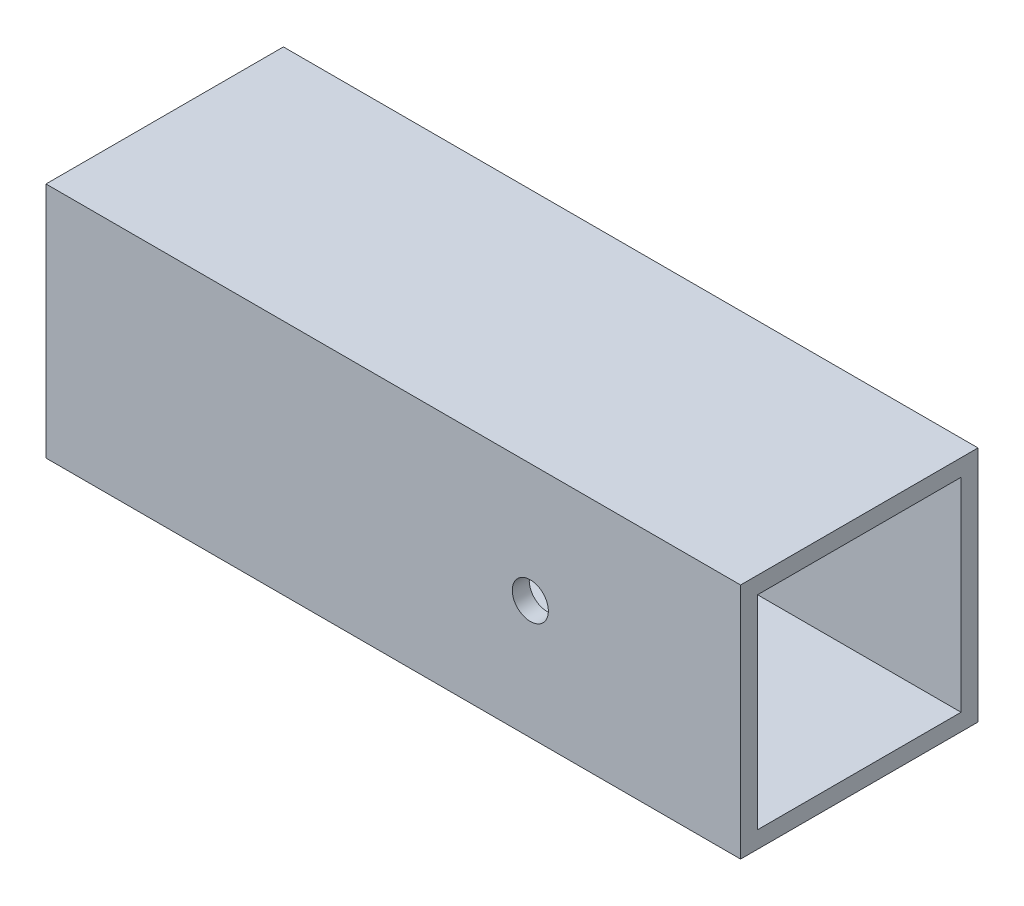
SolidWorks part; units mm, degrees
ref_plane "Front Plane" through (0, 0, 0) normal (0, 0, 1) x (1, 0, 0)
ref_plane "Top Plane" through (0, 0, 0) normal (0, 1, 0) x (1, 0, 0)
ref_plane "Right Plane" through (0, 0, 0) normal (1, 0, 0) x (0, 0, -1)
sketch "Sketch2" plane through (0, 0, 0) normal (1, 0, 0) x (0, 0, -1)
  line L0 (3.175, 3.175) -> (3.175, 41.275)
  line L1 (0, 0) -> (44.45, 0)
  line L2 (0, 0) -> (0, 44.45)
  line L3 (0, 44.45) -> (44.45, 44.45)
  line L4 (44.45, 0) -> (44.45, 44.45)
  line L5 (3.175, 41.275) -> (41.275, 41.275)
  line L6 (41.275, 3.175) -> (41.275, 41.275)
  line L7 (3.175, 3.175) -> (41.275, 3.175)
  dimension "D2" = 44.45
  dimension "D1" = 3.175
extrude "Boss-Extrude1" add sketch "Sketch2" along normal blind 130.048
hole_wizard "1/4 Clearance Hole1" positions "Sketch3" profile "Sketch4" hole size "1/4" standard "ANSI Inch" end condition through all
sketch "Sketch3" plane through (0, 0, 0) normal (0, 0, 1) x (1, 0, 0)
  line L0 (0, 44.45) -> (0, 0) construction
  line L1 (130.048, 44.45) -> (130.048, 0) construction
  point P0 (90.678, 22.225)
  point P5 (0, 22.225)
  dimension "D1" = 39.37
sketch "Sketch4" plane through (90.678, 22.225, 0) normal (1, 0, 0) x (0, -1, 0)
  line L0 (0, 0) -> (0, 44.45)
  line L1 (0, 44.45) -> (3.3782, 44.45)
  line L2 (3.3782, 44.45) -> (3.3782, 0)
  line L5 (3.3782, 0) -> (0, 0)
  line L11 (0, -6.35) -> (0, 107.95) construction
  dimension "Thru Hole Dia." = 6.7564
  dimension "Thru Hole Depth" = 44.45
